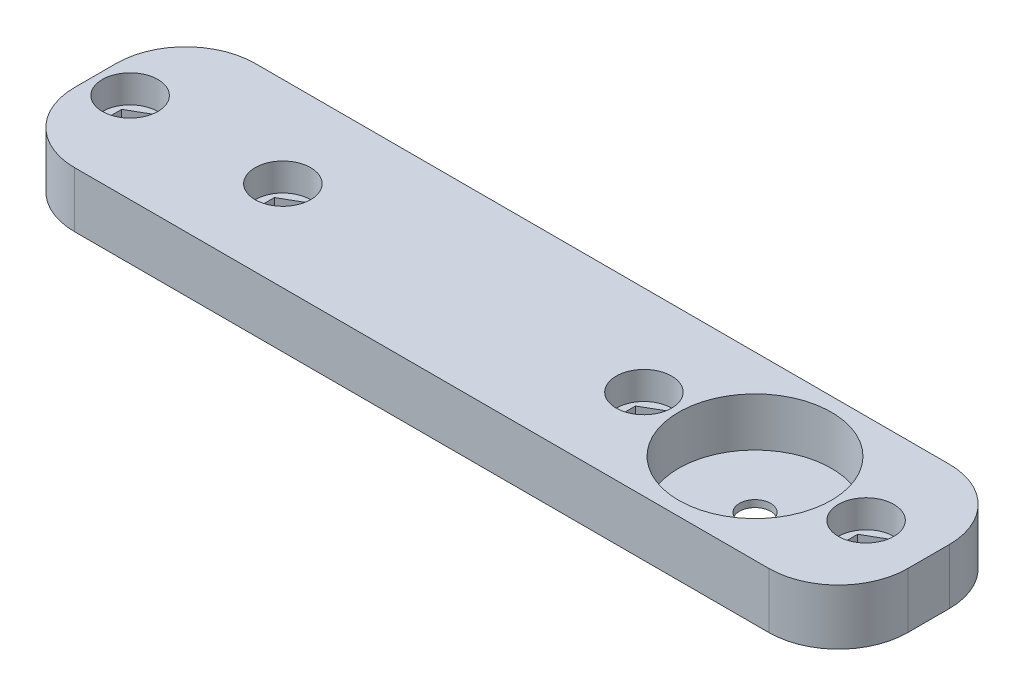
SolidWorks part; units mm, degrees
ref_plane "Front Plane" through (0, 0, 0) normal (0, 0, 1) x (1, 0, 0)
ref_plane "Top Plane" through (0, 0, 0) normal (0, 1, 0) x (1, 0, 0)
ref_plane "Right Plane" through (0, 0, 0) normal (1, 0, 0) x (0, 0, -1)
sketch "Sketch1" plane through (0, 0, 0) normal (0, 1, 0) x (1, 0, 0)
  line L1 (-60, 13) -> (60, 13)
  line L2 (-60, 13) -> (-60, -13)
  line L3 (-60, -13) -> (60, -13)
  line L4 (60, 13) -> (60, -13)
  line L5 (0, -13) -> (0, 13) construction
  line L6 (-60, 0) -> (60, 0) construction
  point P284 (0, 0)
  dimension "D1" = 120
  dimension "D2" = 26
extrude "Boss-Extrude1" add sketch "Sketch1" along normal blind 8
ref_plane "J1_bearing_center" through (35, 0, 0) normal (1, 0, 0) x (0, 0, -1)
sketch "Sketch2" plane through (0, 8, 0) normal (0, 1, 0) x (1, 0, 0)
  line L0 (-4.4, 0) -> (4.4, 0) construction
  line L3 (35, -4.4) -> (35, 4.4) construction
  circle A1 centre (35, 0) radius 11
  dimension "D2" = 22
extrude "Cut-Extrude1" cut sketch "Sketch2" against normal offset from surface (7 mm away) 1 up to face at (0, 0, 0)
sketch "Sketch5" plane through (0, 1, 0) normal (0, 1, 0) x (1, 0, 0)
  circle A0 centre (35, 0) radius 2.25
  dimension "D1" = 4.5
extrude "Cut-Extrude2" cut sketch "Sketch5" against normal through all
sketch "Sketch6" plane through (0, 8, 0) normal (0, 1, 0) x (1, 0, 0)
  line L0 (-4.4, 0) -> (4.4, 0) construction
  line L1 (35, -4.4) -> (35, 4.4) construction
  circle A0 centre (51, 0) radius 4
  circle A2 centre (19, 0) radius 4
  dimension "D1" = 8
  dimension "D2" = 16
extrude "Cut-Extrude3" cut sketch "Sketch6" against normal blind 4
sketch "Sketch7" plane through (0, 4, 0) normal (0, 1, 0) x (1, 0, 0)
  line L0 (35, -4.4) -> (35, 4.4) construction
  line L1 (53.875, -1.6599) -> (53.875, 1.6599)
  line L2 (53.875, 1.6599) -> (51, 3.3198)
  line L3 (51, 3.3198) -> (48.125, 1.6599)
  line L4 (48.125, 1.6599) -> (48.125, -1.6599)
  line L5 (48.125, -1.6599) -> (51, -3.3198)
  line L6 (51, -3.3198) -> (53.875, -1.6599)
  line L7 (19, -3.3198) -> (16.125, -1.6599)
  line L8 (21.875, -1.6599) -> (19, -3.3198)
  line L9 (21.875, 1.6599) -> (21.875, -1.6599)
  line L10 (19, 3.3198) -> (21.875, 1.6599)
  line L11 (16.125, 1.6599) -> (19, 3.3198)
  line L12 (16.125, -1.6599) -> (16.125, 1.6599)
  circle A0 centre (51, 0) radius 2.875 construction
  circle A1 centre (19, 0) radius 2.875 construction
  dimension "D1" = 5.75
extrude "Cut-Extrude4" cut sketch "Sketch7" against normal blind 2.2
hole_wizard "M3 Clearance Hole1" positions "Sketch8" profile "Sketch9" hole size "M3" standard "ISO" end condition up to next
sketch "Sketch8" plane through (0, 1.8, 0) normal (0, 1, 0) x (1, 0, 0)
  point P0 (51, 0)
  point P3 (19, 0)
sketch "Sketch9" plane through (51, 1.8, 0) normal (1, 0, 0) x (0, 0, 1)
  line L0 (0, 0) -> (0, 1.8)
  line L1 (0, 1.8) -> (1.7, 1.8)
  line L2 (1.7, 1.8) -> (1.7, 0)
  line L5 (1.7, 0) -> (0, 0)
  line L11 (0, -6.35) -> (0, 107.95) construction
  dimension "Thru Hole Dia." = 3.4
  dimension "Thru Hole Depth" = 1.8
hole_wizard "M4 Clearance Hole1" positions "Sketch12" profile "Sketch14" hole size "M4" standard "ISO" end condition through all
sketch "Sketch12" plane through (0, 8, 0) normal (0, 1, 0) x (1, 0, 0)
  line L0 (-4.4, 0) -> (4.4, 0) construction
  line L1 (-60, 13) -> (-60, -13) construction
  point P0 (-33, 0)
  point P2 (-55, 0)
  dimension "D1" = 5
  dimension "D2" = 22
sketch "Sketch14" plane through (-33, 8, 0) normal (1, 0, 0) x (0, 0, 1)
  line L0 (0, 0) -> (0, 8)
  line L1 (0, 8) -> (2.25, 8)
  line L2 (2.25, 8) -> (2.25, 0)
  line L5 (2.25, 0) -> (0, 0)
  line L11 (0, -6.35) -> (0, 107.95) construction
  dimension "Thru Hole Dia." = 4.5
  dimension "Thru Hole Depth" = 8
sketch "Sketch10" plane through (0, 8, 0) normal (0, 1, 0) x (1, 0, 0)
  line L0 (-60, 13) -> (-60, -13) construction
  line L1 (-4.4, 0) -> (4.4, 0) construction
  circle A0 centre (-55, 0) radius 4
  circle A1 centre (-33, 0) radius 4
  dimension "D2" = 8
  dimension "D1" = 5
  dimension "D3" = 22
extrude "Cut-Extrude5" cut sketch "Sketch10" against normal blind 4
sketch "Sketch11" plane through (0, 4, 0) normal (0, 1, 0) x (1, 0, 0)
  line L0 (-4.4, 0) -> (4.4, 0) construction
  line L1 (-55, -3.3198) -> (-52.125, -1.6599)
  line L2 (-52.125, -1.6599) -> (-52.125, 1.6599)
  line L3 (-52.125, 1.6599) -> (-55, 3.3198)
  line L4 (-55, 3.3198) -> (-57.875, 1.6599)
  line L5 (-57.875, 1.6599) -> (-57.875, -1.6599)
  line L6 (-57.875, -1.6599) -> (-55, -3.3198)
  line L7 (-35.875, -1.6599) -> (-33, -3.3198)
  line L8 (-33, -3.3198) -> (-30.125, -1.6599)
  line L9 (-30.125, -1.6599) -> (-30.125, 1.6599)
  line L10 (-30.125, 1.6599) -> (-33, 3.3198)
  line L11 (-33, 3.3198) -> (-35.875, 1.6599)
  line L12 (-35.875, 1.6599) -> (-35.875, -1.6599)
  line L13 (0, -4.4) -> (0, 4.4) construction
  circle A0 centre (-55, 0) radius 2.875 construction
  circle A1 centre (-33, 0) radius 2.875 construction
  dimension "D1" = 5.75
  dimension "D2" = 22
  dimension "D3" = 5.75
extrude "Cut-Extrude6" cut sketch "Sketch11" against normal blind 2
fillet "Fillet1" radius 10 4 edges at (60, 4, -13) (60, 4, 13) (-60, 4, 13) (-60, 4, -13)
